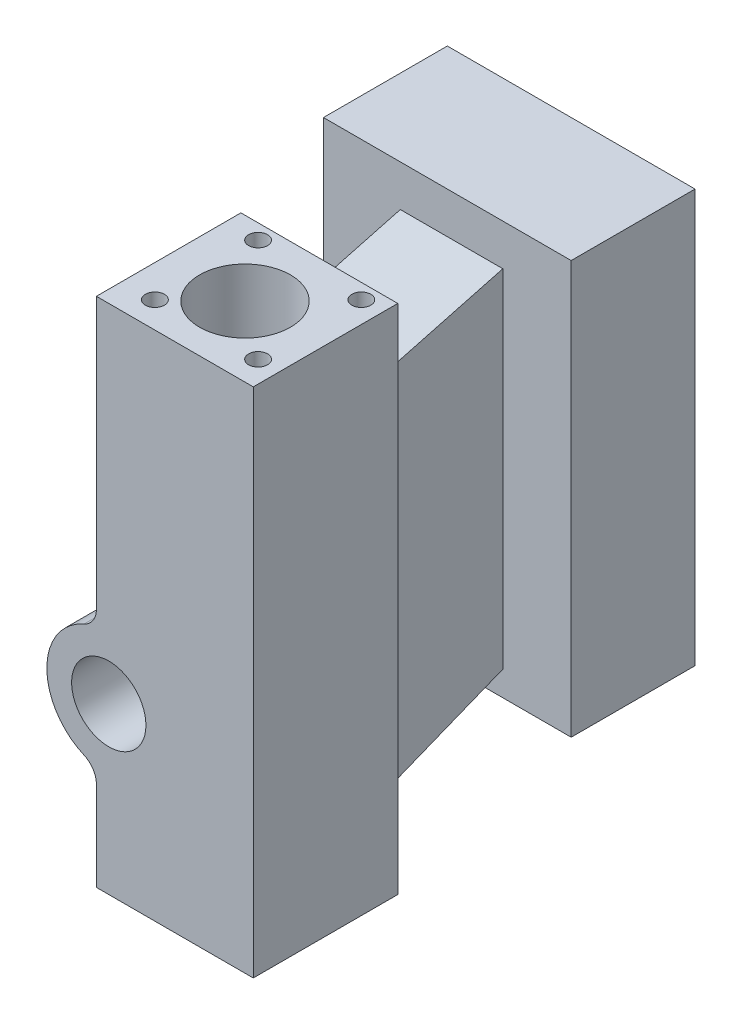
SolidWorks part; units mm, degrees
ref_plane "Front Plane" through (0, 0, 0) normal (0, 0, 1) x (1, 0, 0)
ref_plane "Top Plane" through (0, 0, 0) normal (0, 1, 0) x (1, 0, 0)
ref_plane "Right Plane" through (0, 0, 0) normal (1, 0, 0) x (0, 0, -1)
sketch "Sketch1" plane through (0, 0, 0) normal (0, 0, 1) x (1, 0, 0)
  line L1 (-26.1812, 49.3094) -> (11.8188, 49.3094)
  line L2 (-26.1812, 49.3094) -> (-26.1812, -74.6906)
  line L3 (-26.1812, -74.6906) -> (11.8188, -74.6906)
  line L4 (11.8188, 49.3094) -> (11.8188, -74.6906)
  dimension "D1" = 124
  dimension "D2" = 38
extrude "Boss-Extrude1" add sketch "Sketch1" along normal blind 35
sketch "Sketch2" plane through (0, 0, 35) normal (0, 0, 1) x (1, 0, 0)
  line L4 (11.8188, -74.6906) -> (11.8188, 49.3094) construction
  line L5 (-26.1812, -74.6906) -> (11.8188, -74.6906) construction
  circle A0 centre (-23.1812, -34.6906) radius 15
  dimension "D1" = 35
  dimension "D2" = 40
extrude "Boss-Extrude2" add sketch "Sketch2" against normal blind 34
fillet "Fillet1" radius 5 2 edges at (-26.1812, -19.9937, 18) (-26.1812, -49.3876, 18)
sketch "Sketch3" plane through (0, -74.6906, 0) normal (0, -1, 0) x (1, 0, 0)
  line L0 (11.8188, 35) -> (11.8188, 0) construction
  line L1 (-26.1812, 35) -> (11.8188, 35) construction
  circle A0 centre (-7.1812, 18) radius 11
  dimension "D1" = 19
  dimension "D2" = 17
extrude "Cut-Extrude1" cut sketch "Sketch3" against normal blind 1000
sketch "Sketch4" plane through (0, 0, 35) normal (0, 0, 1) x (1, 0, 0)
  circle A0 centre (-23.1812, -34.6906) radius 9
  arc A1 (-29.1812, -20.9429) -> (-29.1812, -48.4384) centre (-23.1812, -34.6906) ccw construction
  dimension "D1" = 18
sketch "Sketch5" plane through (0, 0, 0) normal (0, 0, -1) x (-1, 0, 0)
  line L1 (-7.2618, 48.6909) -> (17.5691, 48.6909)
  line L2 (-7.2618, 48.6909) -> (-7.2618, -62.513)
  line L3 (-7.2618, -62.513) -> (17.5691, -62.513)
  line L4 (17.5691, 48.6909) -> (17.5691, -62.513)
extrude "Boss-Extrude3" add sketch "Sketch5" along normal blind 30
sketch "Sketch6" plane through (0, 0, -30) normal (0, 0, -1) x (-1, 0, 0)
  line L0 (26.1812, 49.3094) -> (26.1812, -74.6906) construction
  line L1 (-23.8188, 49.3094) -> (36.1812, 49.3094)
  line L2 (-23.8188, 49.3094) -> (-23.8187, -50.6906)
  line L3 (-23.8187, -50.6906) -> (36.1812, -50.6906)
  line L4 (36.1812, 49.3094) -> (36.1812, -50.6906)
  line L5 (-11.8188, 49.3094) -> (26.1812, 49.3094) construction
  dimension "D1" = 60
  dimension "D2" = 100
  dimension "D3" = 10
extrude "Boss-Extrude4" add sketch "Sketch6" along normal blind 30
sketch "Sketch9" plane through (7.2618, 0, 0) normal (1, 0, 0) x (0, 0, -1)
  line L0 (0, 52.6027) -> (0, 31.3094)
  line L1 (0, 31.3094) -> (30, 39.3094)
  line L2 (30, 39.3094) -> (30, 52.6027)
  line L3 (30, 52.6027) -> (0, 52.6027)
  line L4 (0, -56.6906) -> (0, -66.3738)
  line L5 (0, -66.3738) -> (30, -69.2814)
  line L6 (30, -69.2814) -> (30, -44.6906)
  line L7 (30, -44.6906) -> (0, -56.6906)
  line L8 (30, -50.6906) -> (30, 48.6909) construction
  line L9 (0, 49.3094) -> (0, -74.6906) construction
  line L10 (30, -50.6906) -> (30, 49.3094) construction
  line L11 (60, 49.3094) -> (30, 49.3094) construction
  line L12 (-35, 49.3094) -> (0, 49.3094) construction
  line L13 (60, -50.6906) -> (30, -50.6906) construction
  line L14 (-35, -74.6906) -> (0, -74.6906) construction
  dimension "D1" = 10
  dimension "D2" = 18
  dimension "D3" = 6
  dimension "D4" = 18
extrude "Cut-Extrude5" cut sketch "Sketch9" against normal blind 100
sketch "Sketch10" plane through (-36.1812, 0, 0) normal (-1, 0, 0) x (0, 0, 1)
  line L0 (-60, -50.6906) -> (-60, 49.3094) construction
  line L1 (-60, -50.6906) -> (-30, -50.6906) construction
  circle A0 centre (-45, -15.6906) radius 7.5
  dimension "D3" = 15
  dimension "D1" = 15
  dimension "D2" = 35
extrude "Cut-Extrude6" cut sketch "Sketch10" against normal blind 10
sketch "Sketch11" plane through (0, 49.3094, 0) normal (0, 1, 0) x (1, 0, 0)
  circle A0 centre (6.6247, -28.639) radius 2.3015
extrude "Cut-Extrude7" cut sketch "Sketch11" against normal blind 10
pattern_linear "LPattern1" count 2 spacing 25 along (-1, 0, 0) count 2 spacing 25 along (0, 0, -1) of "Cut-Extrude7"
extrude "Вырез-Вытянуть1" cut sketch "Sketch4" against normal blind 17
